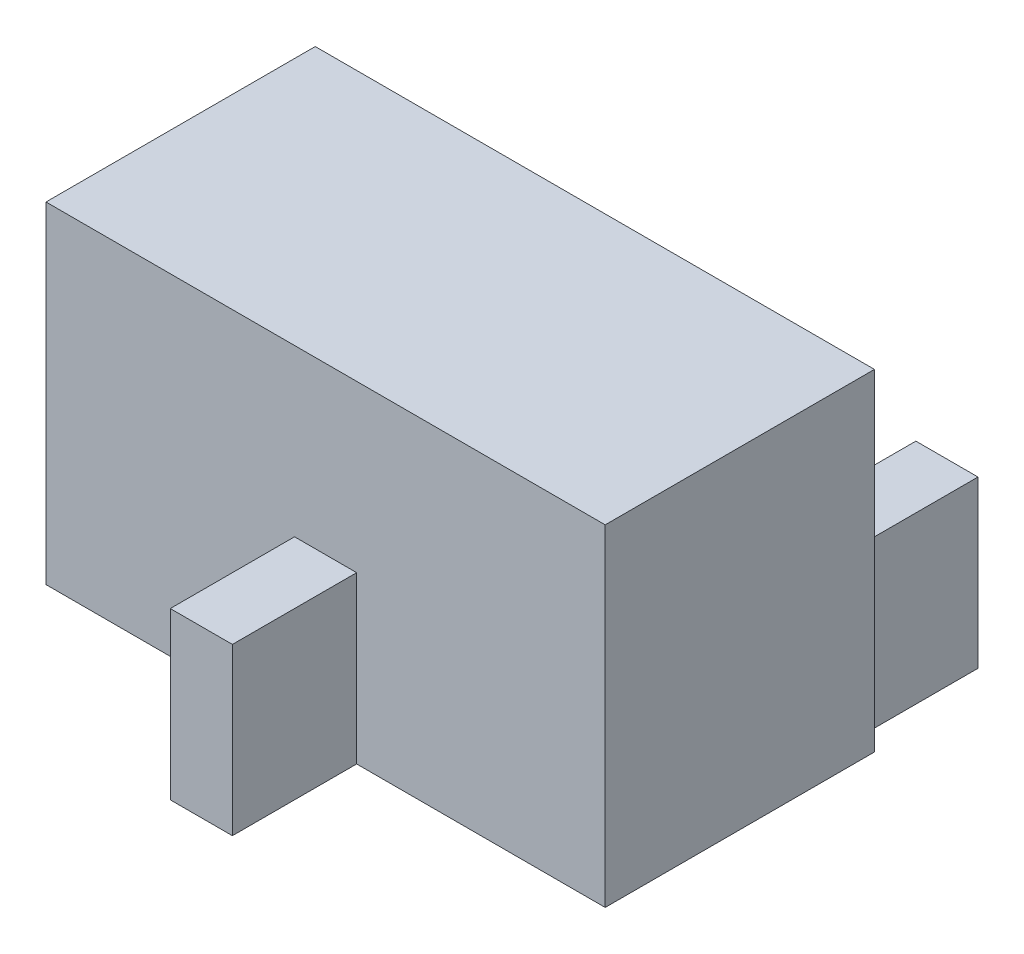
SolidWorks part; units mm, degrees
ref_plane "Спереди" through (0, 0, 0) normal (0, 0, 1) x (1, 0, 0)
ref_plane "Сверху" through (0, 0, 0) normal (0, 1, 0) x (1, 0, 0)
ref_plane "Справа" through (0, 0, 0) normal (1, 0, 0) x (0, 0, -1)
sketch "Эскиз1" plane through (0, 0, 0) normal (0, 1, 0) x (1, 0, 0)
  line L1 (-1.8128, 0.4831) -> (0.8872, 0.4831)
  line L2 (-1.8128, 0.4831) -> (-1.8128, -0.8169)
  line L3 (-1.8128, -0.8169) -> (0.8872, -0.8169)
  line L4 (0.8872, 0.4831) -> (0.8872, -0.8169)
  dimension "D1" = 1.3
  dimension "D2" = 2.7
extrude "Бобышка-Вытянуть1" add sketch "Эскиз1" along normal blind 1.6
sketch "Эскиз2" plane through (0, 0, 0) normal (0, 1, 0) x (1, 0, 0)
  line L0 (-0.4628, 0.4831) -> (-0.4628, 50000.4831) construction
  line L1 (-1.7128, 0.4831) -> (-1.4128, 0.4831)
  line L2 (-1.7128, 0.4831) -> (-1.7128, 1.0831)
  line L3 (-1.7128, 1.0831) -> (-1.4128, 1.0831)
  line L4 (-1.4128, 0.4831) -> (-1.4128, 1.0831)
  line L5 (0.7872, 0.4831) -> (0.4872, 0.4831)
  line L6 (0.7872, 0.4831) -> (0.7872, 1.0831)
  line L7 (0.7872, 1.0831) -> (0.4872, 1.0831)
  line L8 (0.4872, 0.4831) -> (0.4872, 1.0831)
  line L9 (0.8872, 0.4831) -> (-1.8128, 0.4831) construction
  line L10 (-1.8128, -0.8169) -> (0.8872, -0.8169) construction
  line L11 (-0.3128, -1.4169) -> (-0.6128, -1.4169)
  line L12 (-0.3128, -1.4169) -> (-0.3128, -0.8169)
  line L13 (-0.3128, -0.8169) -> (-0.6128, -0.8169)
  line L14 (-0.6128, -1.4169) -> (-0.6128, -0.8169)
  line L15 (-0.3128, -1.4169) -> (-0.6128, -0.8169) construction
  line L16 (-0.3128, -0.8169) -> (-0.6128, -1.4169) construction
  point P14 (-0.4628, 0.4831)
  point P15 (-0.4628, -1.1169)
  dimension "D1" = 0.3
  dimension "D2" = 0.3
  dimension "D3" = 0.6
  dimension "D4" = 0.6
  dimension "D5" = 0.3
  dimension "D6" = 0.6
  dimension "D7" = 1.25
  dimension "D8" = 1.25
extrude "Бобышка-Вытянуть2" add sketch "Эскиз2" along normal blind 0.8
